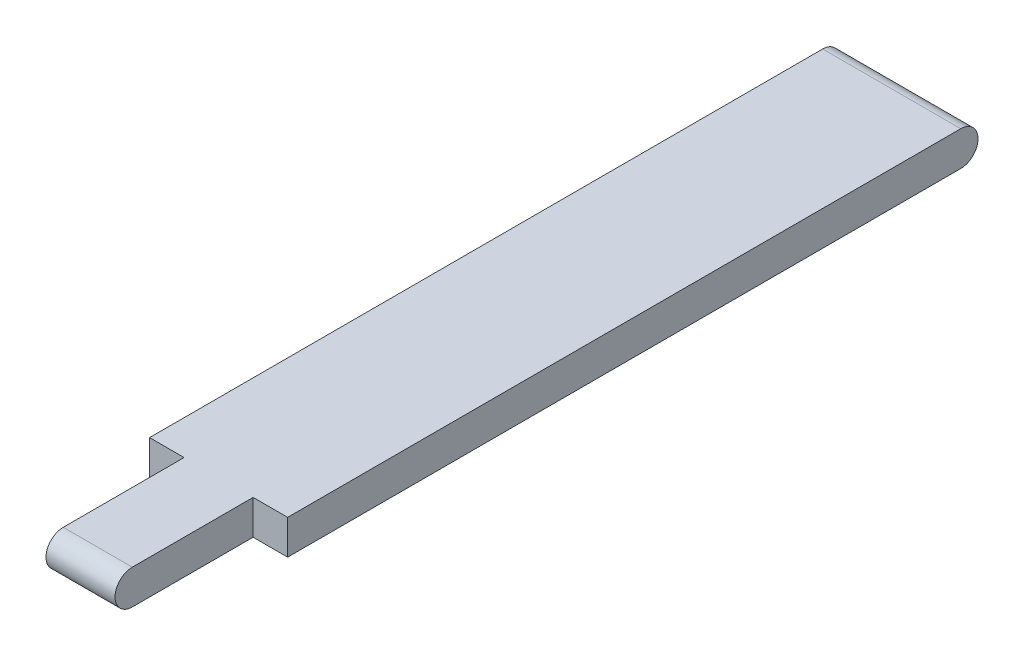
SolidWorks part; units mm, degrees
ref_plane "Front" through (0, 0, 0) normal (0, 0, 1) x (1, 0, 0)
ref_plane "Top" through (0, 0, 0) normal (0, 1, 0) x (1, 0, 0)
ref_plane "Right" through (0, 0, 0) normal (1, 0, 0) x (0, 0, -1)
sketch "草图1" plane through (0, 0, 0) normal (1, 0, 0) x (0, 0, -1)
  line L0 (-23, 0) -> (23, 0) construction
  line L1 (-23, 1) -> (23, 1)
  line L2 (-23, -1) -> (23, -1)
  arc A0 (-23, 1) -> (-23, -1) centre (-23, 0) ccw
  arc A1 (23, -1) -> (23, 1) centre (23, 0) ccw
  point P2 (0, 0)
extrude "凸台-拉伸1" add sketch "草图1" along normal mid plane 8
sketch "草图5" plane through (0, 1, 0) normal (0, 1, 0) x (1, 0, 0)
  line L0 (4, 23) -> (4, -23) construction
  line L1 (-4, -24) -> (-2, -24)
  line L2 (-4, -24) -> (-4, -16)
  line L3 (-4, -16) -> (-2, -16)
  line L4 (4, -24) -> (4, -16)
  line L5 (2, -16) -> (4, -16)
  line L7 (-2, -24) -> (-2, -16)
  line L9 (2, -24) -> (2, -16)
  line L10 (2, -24) -> (4, -24)
  dimension "D1" = 8
  dimension "D2" = 4
  dimension "D3" = 2
extrude "切除-拉伸2" cut sketch "草图5" against normal blind 10
